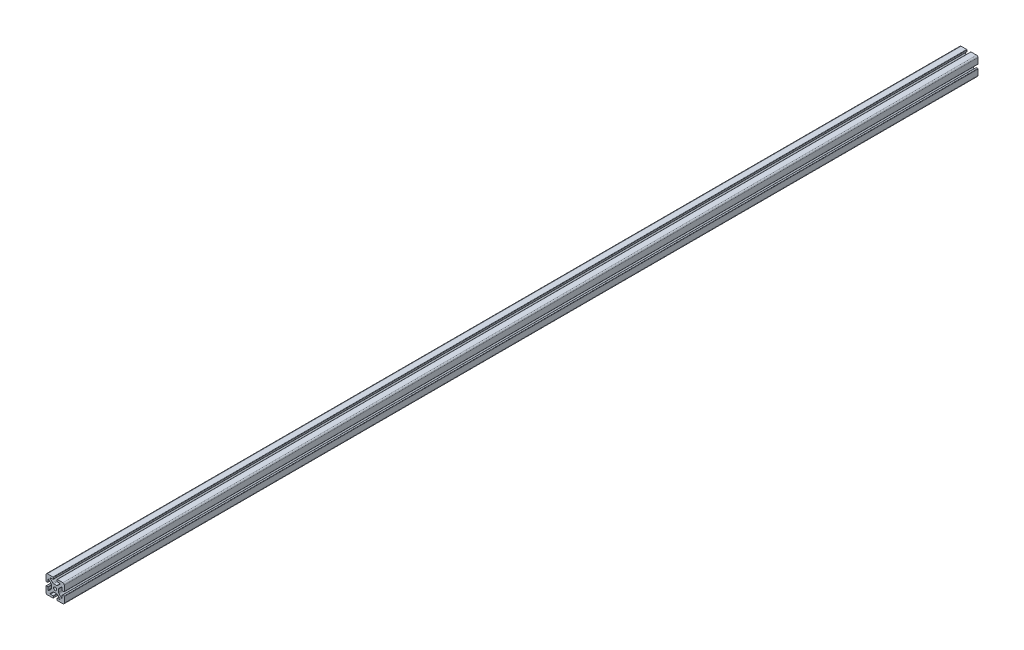
SolidWorks part; units mm, degrees
ref_plane "Front Plane" through (0, 0, 0) normal (0, 0, 1) x (1, 0, 0)
ref_plane "Top Plane" through (0, 0, 0) normal (0, 1, 0) x (1, 0, 0)
ref_plane "Right Plane" through (0, 0, 0) normal (1, 0, 0) x (0, 0, -1)
sketch "Sketch1" plane through (0, 0, 0) normal (0, 0, 1) x (1, 0, 0)
  line L2 (-20, 16.952) -> (-20, 4.7625)
  line L3 (-16.952, 20) -> (-4.7625, 20)
  line L4 (-4.0005, 19.238) -> (-4.0005, 16.2662)
  line L5 (-4.7625, 15.5042) -> (-10.2235, 15.5042)
  line L6 (-10.7623, 14.2034) -> (-5.194, 8.6351)
  line L7 (-14.2034, 10.7623) -> (-8.6351, 5.194)
  line L8 (-15.5042, 10.2235) -> (-15.5042, 4.7625)
  line L9 (-16.2662, 4.0005) -> (-19.238, 4.0005)
  line L11 (-3.0746, 7.7572) -> (3.0746, 7.7572)
  line L12 (-7.7572, 3.0746) -> (-7.7572, -3.0746)
  line L13 (16.2662, 4.0005) -> (19.238, 4.0005)
  line L14 (15.5042, 10.2235) -> (15.5042, 4.7625)
  line L15 (20, 16.952) -> (20, 4.7625)
  line L16 (16.952, 20) -> (4.7625, 20)
  line L17 (4.0005, 19.238) -> (4.0005, 16.2662)
  line L18 (4.7625, 15.5042) -> (10.2235, 15.5042)
  line L19 (7.7572, 3.0746) -> (7.7572, -3.0746)
  line L20 (10.7623, 14.2034) -> (5.194, 8.6351)
  line L21 (14.2034, 10.7623) -> (8.6351, 5.194)
  line L22 (-16.2662, -4.0005) -> (-19.238, -4.0005)
  line L23 (-15.5042, -10.2235) -> (-15.5042, -4.7625)
  line L24 (-14.2034, -10.7623) -> (-8.6351, -5.194)
  line L25 (-10.7623, -14.2034) -> (-5.194, -8.6351)
  line L26 (-4.7625, -15.5042) -> (-10.2235, -15.5042)
  line L27 (-4.0005, -19.238) -> (-4.0005, -16.2662)
  line L28 (-16.952, -20) -> (-4.7625, -20)
  line L29 (-20, -16.952) -> (-20, -4.7625)
  line L30 (20, -16.952) -> (20, -4.7625)
  line L31 (16.952, -20) -> (4.7625, -20)
  line L32 (4.0005, -19.238) -> (4.0005, -16.2662)
  line L33 (4.7625, -15.5042) -> (10.2235, -15.5042)
  line L34 (10.7623, -14.2034) -> (5.194, -8.6351)
  line L35 (14.2034, -10.7623) -> (8.6351, -5.194)
  line L36 (15.5042, -10.2235) -> (15.5042, -4.7625)
  line L37 (16.2662, -4.0005) -> (19.238, -4.0005)
  line L38 (-3.0746, -7.7572) -> (3.0746, -7.7572)
  circle A0 centre (0, 0) radius 3.4036
  arc A1 (-20, 16.952) -> (-16.952, 20) centre (-16.952, 16.952) cw
  arc A2 (-14.2034, 10.7623) -> (-15.5042, 10.2235) centre (-14.7422, 10.2235) ccw
  arc A3 (-10.2235, 15.5042) -> (-10.7623, 14.2034) centre (-10.2235, 14.7422) ccw
  arc A4 (-4.7625, 20) -> (-4.0005, 19.238) centre (-4.7625, 19.238) cw
  arc A5 (-20, 4.7625) -> (-19.238, 4.0005) centre (-19.238, 4.7625) ccw
  arc A6 (-15.5042, 4.7625) -> (-16.2662, 4.0005) centre (-16.2662, 4.7625) cw
  arc A7 (-4.0005, 16.2662) -> (-4.7625, 15.5042) centre (-4.7625, 16.2662) cw
  arc A8 (-3.0746, 7.7572) -> (-5.194, 8.6351) centre (-3.0746, 10.7544) cw
  arc A9 (-7.7572, 3.0746) -> (-8.6351, 5.194) centre (-10.7544, 3.0746) ccw
  arc A10 (15.5042, 4.7625) -> (16.2662, 4.0005) centre (16.2662, 4.7625) ccw
  arc A11 (20, 4.7625) -> (19.238, 4.0005) centre (19.238, 4.7625) cw
  arc A12 (20, 16.952) -> (16.952, 20) centre (16.952, 16.952) ccw
  arc A13 (4.7625, 20) -> (4.0005, 19.238) centre (4.7625, 19.238) ccw
  arc A14 (4.0005, 16.2662) -> (4.7625, 15.5042) centre (4.7625, 16.2662) ccw
  arc A15 (3.0746, 7.7572) -> (5.194, 8.6351) centre (3.0746, 10.7544) ccw
  arc A16 (7.7572, 3.0746) -> (8.6351, 5.194) centre (10.7544, 3.0746) cw
  arc A17 (14.2034, 10.7623) -> (15.5042, 10.2235) centre (14.7422, 10.2235) cw
  arc A18 (10.2235, 15.5042) -> (10.7623, 14.2034) centre (10.2235, 14.7422) cw
  arc A19 (-7.7572, -3.0746) -> (-8.6351, -5.194) centre (-10.7544, -3.0746) cw
  arc A20 (-3.0746, -7.7572) -> (-5.194, -8.6351) centre (-3.0746, -10.7544) ccw
  arc A21 (-4.0005, -16.2662) -> (-4.7625, -15.5042) centre (-4.7625, -16.2662) ccw
  arc A22 (-15.5042, -4.7625) -> (-16.2662, -4.0005) centre (-16.2662, -4.7625) ccw
  arc A23 (-20, -4.7625) -> (-19.238, -4.0005) centre (-19.238, -4.7625) cw
  arc A24 (-4.7625, -20) -> (-4.0005, -19.238) centre (-4.7625, -19.238) ccw
  arc A25 (-10.2235, -15.5042) -> (-10.7623, -14.2034) centre (-10.2235, -14.7422) cw
  arc A26 (-14.2034, -10.7623) -> (-15.5042, -10.2235) centre (-14.7422, -10.2235) cw
  arc A27 (-20, -16.952) -> (-16.952, -20) centre (-16.952, -16.952) ccw
  arc A28 (20, -16.952) -> (16.952, -20) centre (16.952, -16.952) cw
  arc A29 (14.2034, -10.7623) -> (15.5042, -10.2235) centre (14.7422, -10.2235) ccw
  arc A30 (10.2235, -15.5042) -> (10.7623, -14.2034) centre (10.2235, -14.7422) ccw
  arc A31 (4.7625, -20) -> (4.0005, -19.238) centre (4.7625, -19.238) cw
  arc A32 (20, -4.7625) -> (19.238, -4.0005) centre (19.238, -4.7625) ccw
  arc A33 (15.5042, -4.7625) -> (16.2662, -4.0005) centre (16.2662, -4.7625) cw
  arc A34 (4.0005, -16.2662) -> (4.7625, -15.5042) centre (4.7625, -16.2662) cw
  arc A35 (3.0746, -7.7572) -> (5.194, -8.6351) centre (3.0746, -10.7544) cw
  arc A36 (7.7572, -3.0746) -> (8.6351, -5.194) centre (10.7544, -3.0746) ccw
extrude "Boss-Extrude1" add sketch "Sketch1" along normal mid plane 2000
